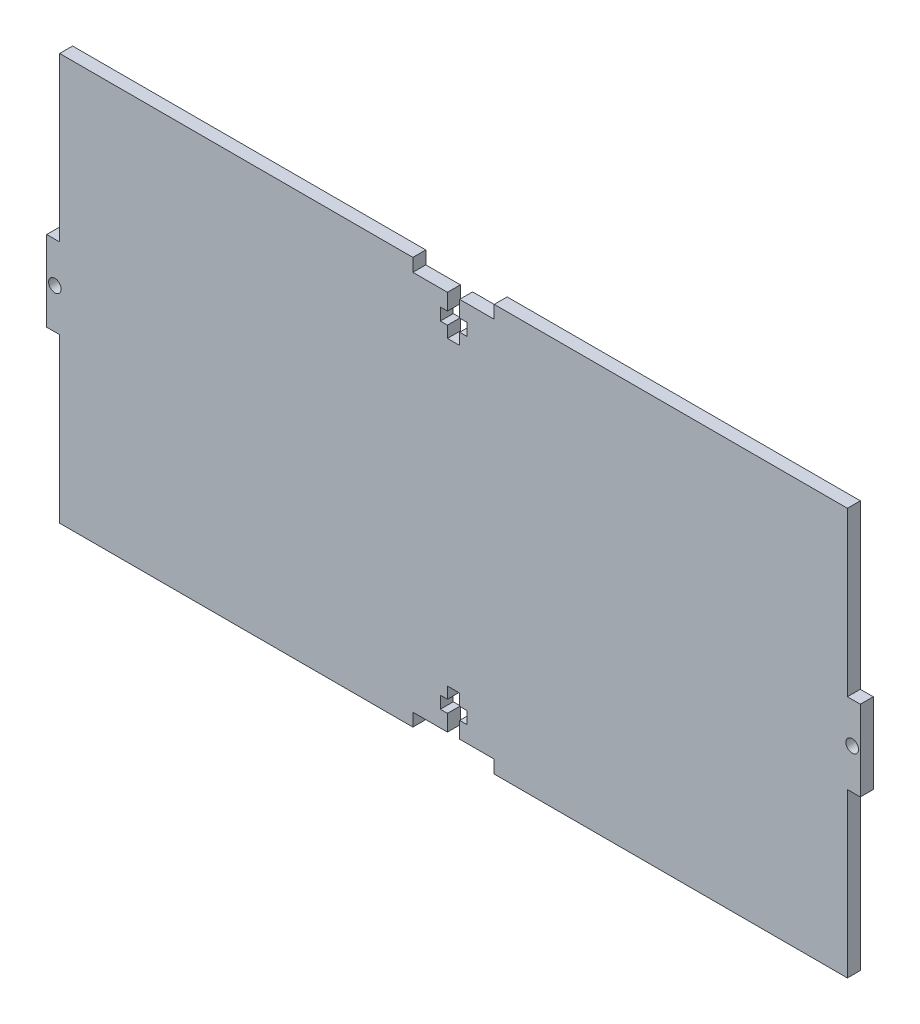
SolidWorks part; units mm, degrees
ref_plane "Front Plane" through (0, 0, 0) normal (0, 0, 1) x (1, 0, 0)
ref_plane "Top Plane" through (0, 0, 0) normal (0, 1, 0) x (1, 0, 0)
ref_plane "Right Plane" through (0, 0, 0) normal (1, 0, 0) x (0, 0, -1)
sketch "Sketch1" plane through (0, 0, 0) normal (0, 0, 1) x (1, 0, 0)
  line L0 (0, 40) -> (0, -40) construction
  line L5 (-100, -50) -> (100, 50) construction
  line L6 (-100, 50) -> (100, -50) construction
  line L7 (-100, 0) -> (100, 0) construction
  line L32 (-100, 50) -> (100, 50)
  line L35 (100, 50) -> (100, -50)
  line L36 (100, -50) -> (-100, -50)
  line L37 (-100, -50) -> (-100, 50)
  point P0 (0, 0)
  dimension "D1" = 200
  dimension "D2" = 100
extrude "Boss-Extrude2" add sketch "Sketch1" along normal blind 3.18
sketch "Sketch2" plane through (0, 0, 3.18) normal (0, 0, 1) x (1, 0, 0)
  line L0 (0, -50) -> (0, 50) construction
  line L1 (-123.0225, 0) -> (147.0753, 0) construction
  line L2 (100, 50) -> (-100, 50) construction
  line L4 (-10, 50) -> (-10, 46.82)
  line L5 (-10, 46.82) -> (-1.5, 46.82)
  line L6 (10, 50) -> (10, 46.82)
  line L7 (1.5, 46.82) -> (10, 46.82)
  line L9 (-1.5, 46.82) -> (-1.5, 42.82)
  line L10 (-1.5, 37) -> (1.5, 37)
  line L11 (1.5, 46.82) -> (1.5, 42.82)
  line L12 (-3.25, 42.82) -> (-1.5, 42.82)
  line L13 (-3.25, 42.82) -> (-3.25, 39.82)
  line L14 (-3.25, 39.82) -> (-1.5, 39.82)
  line L15 (3.25, 42.82) -> (3.25, 39.82)
  line L16 (1.5, 42.82) -> (3.25, 42.82)
  line L17 (-1.5, 39.82) -> (-1.5, 37)
  line L18 (1.5, 39.82) -> (1.5, 37)
  line L19 (1.5, 39.82) -> (3.25, 39.82)
  line L20 (-10, 50) -> (10, 50)
  line L21 (-100, -50) -> (100, -50) construction
  line L22 (-100, 50) -> (-100, -50) construction
  line L23 (-100, 9.875) -> (-96.82, 9.875)
  line L24 (-100, 9.875) -> (-100, 50)
  line L25 (-100, 50) -> (-96.82, 50)
  line L26 (-96.82, 9.875) -> (-96.82, 50)
  line L28 (-100, -9.875) -> (-96.82, -9.875)
  line L29 (-100, -9.875) -> (-100, -50)
  line L30 (-100, -50) -> (-96.82, -50)
  line L31 (-96.82, -9.875) -> (-96.82, -50)
  circle A0 centre (-98, 0) radius 1.55
  dimension "D11" = 3.1
  dimension "D12" = 2
  dimension "D1" = 4
  dimension "D2" = 3
  dimension "D3" = 3
  dimension "D4" = 20
  dimension "D5" = 6.5
  dimension "D6" = 3.18
  dimension "D7" = 13
  dimension "D8" = 19.75
  dimension "D9" = 3.18
  dimension "D10" = 3.18
extrude "Cut-Extrude1" cut sketch "Sketch2" against normal through all
mirror "Mirror1" about plane through (0, 0, 0) normal (0, 1, 0) of "Cut-Extrude1"
mirror "Mirror2" about plane through (0, 0, 0) normal (1, 0, 0) of "Cut-Extrude1"
